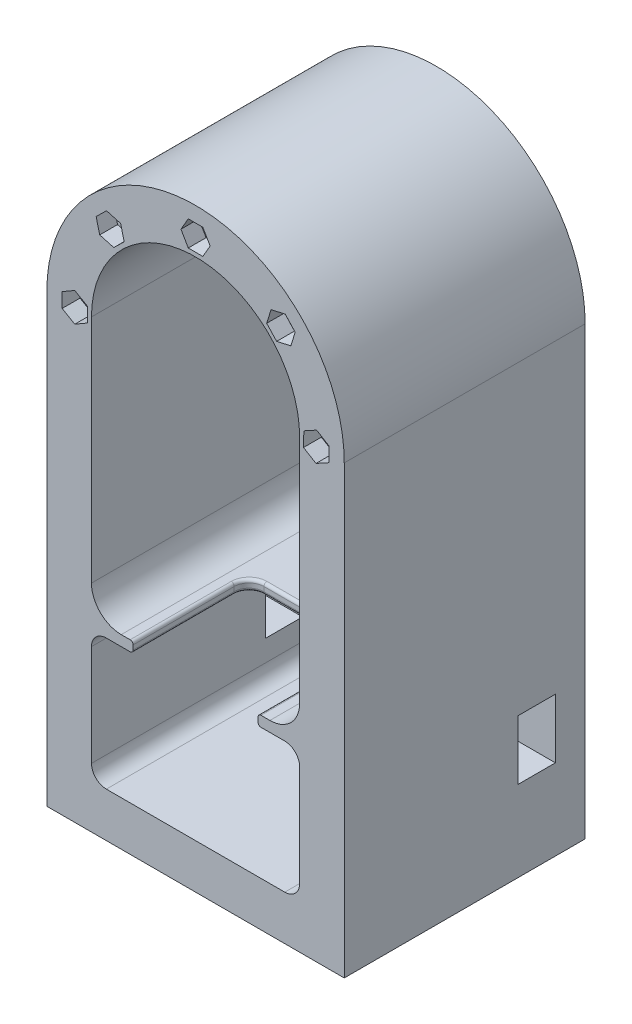
SolidWorks part; units mm, degrees
ref_plane "Alzado" through (0, 0, 0) normal (0, 0, 1) x (1, 0, 0)
ref_plane "Planta" through (0, 0, 0) normal (0, 1, 0) x (1, 0, 0)
ref_plane "Vista lateral" through (0, 0, 0) normal (1, 0, 0) x (0, 0, -1)
sketch "Croquis1" plane through (0, 0, 0) normal (0, 0, 1) x (1, 0, 0)
  line L0 (0, 0) -> (0, -113) construction
  line L1 (50, 0) -> (50, -150)
  line L2 (-35, 0) -> (-35, -77.5)
  line L4 (0, -150) -> (-50, -150)
  line L5 (-50, 0) -> (-50, -150)
  line L6 (0, -150) -> (50, -150)
  line L12 (-25, -87.5) -> (25, -87.5)
  line L13 (35, 0) -> (35, -135) construction
  line L15 (35, 0) -> (35, -77.5)
  line L16 (-35, 0) -> (-35, -135) construction
  line L17 (0, -135) -> (-35, -135) construction
  line L18 (0, -135) -> (35, -135) construction
  arc A0 (50, 0) -> (-50, 0) centre (0, 0) ccw
  arc A1 (35, 0) -> (-35, 0) centre (0, 0) ccw
  arc A2 (35, -77.5) -> (25, -87.5) centre (25, -77.5) cw
  arc A3 (-35, -77.5) -> (-25, -87.5) centre (-25, -77.5) ccw
  dimension "D1" = 100
  dimension "D3" = 10
  dimension "D2" = 113
  dimension "D4" = 15
extrude "Saliente-Extruir1" add sketch "Croquis1" along normal blind 81
sketch "Croquis2" plane through (0, 0, 0) normal (0, 0, -1) x (-1, 0, 0)
  line L0 (0, 35) -> (0, 50) construction
  line L1 (-50, 0) -> (-35, 0) construction
  line L2 (35, 0) -> (50, 0) construction
  line L3 (-50, -38.75) -> (-35, -38.75) construction
  line L4 (-50, -150) -> (-50, 0) construction
  line L5 (-35, -77.5) -> (-35, 0) construction
  line L6 (35, -38.75) -> (50, -38.75) construction
  line L7 (35, 0) -> (35, -77.5) construction
  line L8 (50, 0) -> (50, -150) construction
  line L9 (-42.5, -38.75) -> (-42.5, -150) construction
  line L10 (50, -150) -> (-50, -150) construction
  line L12 (-35, -135) -> (-50, -135) construction
  line L13 (35, -135) -> (50, -135) construction
  line L15 (4.9075, 42.5) -> (2.4537, 46.75)
  line L16 (2.4537, 46.75) -> (-2.4537, 46.75)
  line L17 (-2.4537, 46.75) -> (-4.9075, 42.5)
  line L18 (-4.9075, 42.5) -> (-2.4537, 38.25)
  line L19 (-2.4537, 38.25) -> (2.4537, 38.25)
  line L20 (2.4537, 38.25) -> (4.9075, 42.5)
  line L21 (-42.5, 4.9075) -> (-46.75, 2.4537)
  line L22 (-46.75, 2.4537) -> (-46.75, -2.4537)
  line L23 (-46.75, -2.4537) -> (-42.5, -4.9075)
  line L24 (-42.5, -4.9075) -> (-38.25, -2.4537)
  line L25 (-38.25, -2.4537) -> (-38.25, 2.4537)
  line L26 (-38.25, 2.4537) -> (-42.5, 4.9075)
  line L27 (42.5, 4.9075) -> (38.25, 2.4537)
  line L28 (38.25, 2.4537) -> (38.25, -2.4537)
  line L29 (38.25, -2.4537) -> (42.5, -4.9075)
  line L30 (42.5, -4.9075) -> (46.75, -2.4537)
  line L31 (46.75, -2.4537) -> (46.75, 2.4537)
  line L32 (46.75, 2.4537) -> (42.5, 4.9075)
  line L33 (-42.5, -33.8425) -> (-46.75, -36.2963)
  line L34 (-46.75, -36.2963) -> (-46.75, -41.2037)
  line L35 (-46.75, -41.2037) -> (-42.5, -43.6575)
  line L36 (-42.5, -43.6575) -> (-38.25, -41.2037)
  line L37 (-38.25, -41.2037) -> (-38.25, -36.2963)
  line L38 (-38.25, -36.2963) -> (-42.5, -33.8425)
  line L39 (42.5, -33.8425) -> (38.25, -36.2963)
  line L40 (38.25, -36.2963) -> (38.25, -41.2037)
  line L41 (38.25, -41.2037) -> (42.5, -43.6575)
  line L42 (42.5, -43.6575) -> (46.75, -41.2037)
  line L43 (46.75, -41.2037) -> (46.75, -36.2963)
  line L44 (46.75, -36.2963) -> (42.5, -33.8425)
  line L45 (-42.5, -130.0925) -> (-46.75, -132.5463)
  line L46 (-46.75, -132.5463) -> (-46.75, -137.4537)
  line L47 (-46.75, -137.4537) -> (-42.5, -139.9075)
  line L48 (-42.5, -139.9075) -> (-38.25, -137.4537)
  line L49 (-38.25, -137.4537) -> (-38.25, -132.5463)
  line L50 (-38.25, -132.5463) -> (-42.5, -130.0925)
  line L51 (42.5, -139.9075) -> (46.75, -137.4537)
  line L52 (46.75, -137.4537) -> (46.75, -132.5463)
  line L53 (46.75, -132.5463) -> (42.5, -130.0925)
  line L54 (42.5, -130.0925) -> (38.25, -132.5463)
  line L55 (38.25, -132.5463) -> (38.25, -137.4537)
  line L56 (38.25, -137.4537) -> (42.5, -139.9075)
  arc A0 (35, 0) -> (-35, 0) centre (0, 0) ccw construction
  arc A1 (50, 0) -> (-50, 0) centre (0, 0) ccw construction
  circle A2 centre (0, 42.5) radius 4.25 construction
  circle A3 centre (-42.5, 0) radius 4.25 construction
  circle A4 centre (42.5, 0) radius 4.25 construction
  circle A5 centre (-42.5, -38.75) radius 4.25 construction
  circle A6 centre (42.5, -38.75) radius 4.25 construction
  circle A7 centre (-42.5, -135) radius 4.25 construction
  circle A8 centre (42.5, -135) radius 4.25 construction
  dimension "D1" = 8.5
  dimension "D2" = 8.5
  dimension "D3" = 8.5
  dimension "D4" = 8.5
  dimension "D5" = 8.5
  dimension "D6" = 8.5
  dimension "D7" = 8.5
  dimension "D8" = 15
extrude "Cortar-Extruir1" cut sketch "Croquis2" against normal blind 6
sketch "Croquis3" plane through (0, 0, 81) normal (0, 0, 1) x (1, 0, 0)
  line L1 (-15.5, -97.5) -> (15.5, -97.5)
  line L2 (-15.5, -97.5) -> (-15.5, -128.5)
  line L3 (-15.5, -128.5) -> (15.5, -128.5)
  line L4 (15.5, -97.5) -> (15.5, -128.5)
  line L5 (-15.5, -97.5) -> (15.5, -128.5) construction
  line L6 (-15.5, -128.5) -> (15.5, -97.5) construction
  circle A0 centre (-15.5, -97.5) radius 2
  circle A1 centre (15.5, -97.5) radius 2
  circle A2 centre (15.5, -128.5) radius 2
  circle A3 centre (-15.5, -128.5) radius 2
  point P0 (0, -113)
  dimension "D3" = 4
  dimension "D1" = 113
  dimension "D2" = 31
extrude "Cortar-Extruir2" cut sketch "Croquis3" against normal up to surface (81 mm away) contours A0 | A3 | A2 | A1 up to face at (-42.5, -135, 0)
sketch "Croquis4" plane through (0, 0, 0) normal (0, 0, -1) x (-1, 0, 0)
  circle A0 centre (-15.5, -97.5) radius 4
  circle A1 centre (15.5, -97.5) radius 4
  circle A2 centre (-15.5, -128.5) radius 4
  circle A3 centre (15.5, -128.5) radius 4
  dimension "D1" = 8
extrude "Cortar-Extruir4" cut sketch "Croquis4" against normal blind 6
sketch "Croquis6" plane through (0, 0, 81) normal (0, 0, 1) x (1, 0, 0)
  line L0 (0, 0) -> (0, -113) construction
  line L2 (-30, -91) -> (30, -91)
  line L3 (-35, -96) -> (-35, -130)
  line L4 (-30, -135) -> (30, -135)
  line L5 (35, -96) -> (35, -130)
  line L6 (-35, -91) -> (35, -135) construction
  line L7 (-35, -135) -> (35, -91) construction
  arc A0 (30, -91) -> (35, -96) centre (30, -96) cw
  arc A1 (35, -130) -> (30, -135) centre (30, -130) cw
  arc A2 (-35, -130) -> (-30, -135) centre (-30, -130) ccw
  arc A3 (-30, -91) -> (-35, -96) centre (-30, -96) ccw
  dimension "D4" = 5
  dimension "D1" = 113
  dimension "D2" = 44
  dimension "D3" = 70
extrude "Cortar-Extruir5" cut sketch "Croquis6" against normal blind 71
sketch "Croquis7" plane through (0, 0, 81) normal (0, 0, 1) x (1, 0, 0)
  circle A0 centre (0, 0) radius 40.605
  circle A1 centre (0, 40.605) radius 2.75
  circle A2 centre (28.7121, 28.7121) radius 2.75
  circle A3 centre (40.605, 0) radius 2.75
  circle A4 centre (28.7121, -28.7121) radius 2.75
  circle A5 centre (0, -40.605) radius 2.75
  circle A6 centre (-28.7121, -28.7121) radius 2.75
  circle A7 centre (-40.605, 0) radius 2.75
  circle A8 centre (-28.7121, 28.7121) radius 2.75
  point P22 (0, 0)
  dimension "D1" = 81.21
  dimension "D2" = 5.5
  dimension "D3" = 8
extrude "Cortar-Extruir6" cut sketch "Croquis7" against normal blind 71 contours A6 | A7 | A8 | A1 | A2 | A3 | A4 | A5
sketch "Croquis8" plane through (0, 0, 81) normal (0, 0, 1) x (1, 0, 0)
  line L1 (4.9075, 40.605) -> (2.4537, 44.855)
  line L2 (2.4537, 44.855) -> (-2.4537, 44.855)
  line L3 (-2.4537, 44.855) -> (-4.9075, 40.605)
  line L4 (-4.9075, 40.605) -> (-2.4537, 36.355)
  line L5 (-2.4537, 36.355) -> (2.4537, 36.355)
  line L6 (2.4537, 36.355) -> (4.9075, 40.605)
  line L7 (-23.9873, 27.3855) -> (-25.2009, 32.1406)
  line L8 (-25.2009, 32.1406) -> (-29.9257, 33.4671)
  line L9 (-29.9257, 33.4671) -> (-33.4369, 30.0386)
  line L10 (-33.4369, 30.0386) -> (-32.2233, 25.2836)
  line L11 (-32.2233, 25.2836) -> (-27.4985, 23.957)
  line L12 (-27.4985, 23.957) -> (-23.9873, 27.3855)
  line L13 (32.0499, 25.1146) -> (33.4965, 29.804)
  line L14 (33.4965, 29.804) -> (30.1587, 33.4015)
  line L15 (30.1587, 33.4015) -> (25.3742, 32.3096)
  line L16 (25.3742, 32.3096) -> (23.9276, 27.6201)
  line L17 (23.9276, 27.6201) -> (27.2655, 24.0226)
  line L18 (27.2655, 24.0226) -> (32.0499, 25.1146)
  line L19 (-40.605, -4.9075) -> (-36.355, -2.4537)
  line L20 (-36.355, -2.4537) -> (-36.355, 2.4537)
  line L21 (-36.355, 2.4537) -> (-40.605, 4.9075)
  line L22 (-40.605, 4.9075) -> (-44.855, 2.4537)
  line L23 (-44.855, 2.4537) -> (-44.855, -2.4537)
  line L24 (-44.855, -2.4537) -> (-40.605, -4.9075)
  line L25 (44.8017, -2.5439) -> (44.9064, 2.3625)
  line L26 (44.9064, 2.3625) -> (40.7097, 4.9064)
  line L27 (40.7097, 4.9064) -> (36.4083, 2.5439)
  line L28 (36.4083, 2.5439) -> (36.3036, -2.3625)
  line L29 (36.3036, -2.3625) -> (40.5003, -4.9064)
  line L30 (40.5003, -4.9064) -> (44.8017, -2.5439)
  circle A0 centre (0, 40.605) radius 4.25 construction
  circle A1 centre (-28.7121, 28.7121) radius 4.25 construction
  circle A2 centre (28.7121, 28.7121) radius 4.25 construction
  circle A4 centre (-40.605, 0) radius 4.25 construction
  circle A5 centre (40.605, 0) radius 4.25 construction
  dimension "D1" = 8.5
  dimension "D2" = 8.5
  dimension "D3" = 8.5
  dimension "D4" = 8.5
  dimension "D5" = 8.5
extrude "Cortar-Extruir7" cut sketch "Croquis8" against normal blind 6
sketch "Croquis9" plane through (0, -87.5, 0) normal (0, 1, 0) x (1, 0, 0)
  line L0 (-25, -81) -> (25, -81) construction
  line L1 (-21, -120) -> (21, -120)
  line L2 (-21, -120) -> (-21, -47)
  line L3 (-16, -42) -> (16, -42)
  line L4 (21, -120) -> (21, -47)
  line L5 (-21, -120) -> (21, -42) construction
  line L6 (-21, -42) -> (21, -120) construction
  line L7 (-25, 0) -> (25, 0) construction
  arc A0 (16, -42) -> (21, -47) centre (16, -47) cw
  arc A1 (-21, -47) -> (-16, -42) centre (-16, -47) cw
  point P0 (0, -81)
  dimension "D3" = 5
  dimension "D1" = 42
  dimension "D2" = 42
extrude "Cortar-Extruir8" cut sketch "Croquis9" against normal blind 6
fillet "Redondeo2" radius 1 10 edges at (21, -91, 64) (19.5355, -91, 43.4645) (-21, -91, 64) (-19.5355, -91, 43.4645) (21, -87.5, 64) (19.5355, -87.5, 43.4645) (-21, -87.5, 64) (-19.5355, -87.5, 43.4645) (0, -91, 42) (0, -87.5, 42)
sketch "Croquis10" plane through (0, 0, 0) normal (0, 0, -1) x (-1, 0, 0)
  line L0 (-2.4537, 46.75) -> (2.4537, 38.25) construction
  line L1 (38.25, 2.4537) -> (46.75, -2.4537) construction
  line L2 (38.25, -36.2963) -> (46.75, -41.2037) construction
  line L3 (-38.25, -2.4537) -> (-46.75, 2.4537) construction
  line L4 (-38.25, -41.2037) -> (-46.75, -36.2963) construction
  line L5 (-46.75, -132.5463) -> (-38.25, -137.4537) construction
  line L6 (38.25, -137.4537) -> (46.75, -132.5463) construction
  circle A0 centre (0, 42.5) radius 3
  circle A1 centre (-42.5, 0) radius 3
  circle A2 centre (42.5, 0) radius 3
  circle A3 centre (42.5, -38.75) radius 3
  circle A4 centre (-42.5, -38.75) radius 3
  circle A5 centre (-42.5, -135) radius 3
  circle A6 centre (42.5, -135) radius 3
  dimension "D1" = 6
extrude "Cortar-Extruir9" cut sketch "Croquis10" against normal blind 71
sketch "Croquis15" plane through (50, 0, 0) normal (1, 0, 0) x (0, 0, -1)
  line L0 (-63.165, -112.8399) -> (0, -112.8399) construction
  line L1 (0, -150) -> (0, 0) construction
  line L3 (-22.5, -102.8399) -> (-10, -102.8399)
  line L4 (-22.5, -102.8399) -> (-22.5, -122.8399)
  line L5 (-22.5, -122.8399) -> (-10, -122.8399)
  line L6 (-10, -102.8399) -> (-10, -122.8399)
  line L7 (-22.5, -102.8399) -> (-10, -122.8399) construction
  line L8 (-22.5, -122.8399) -> (-10, -102.8399) construction
  point P4 (-16.25, -112.8399)
  dimension "D1" = 10
  dimension "D2" = 12.5
  dimension "D3" = 20
extrude "Cortar-Extruir10" cut sketch "Croquis15" against normal up to surface (100 mm away) up to face at (-50, -75, 40.5)
